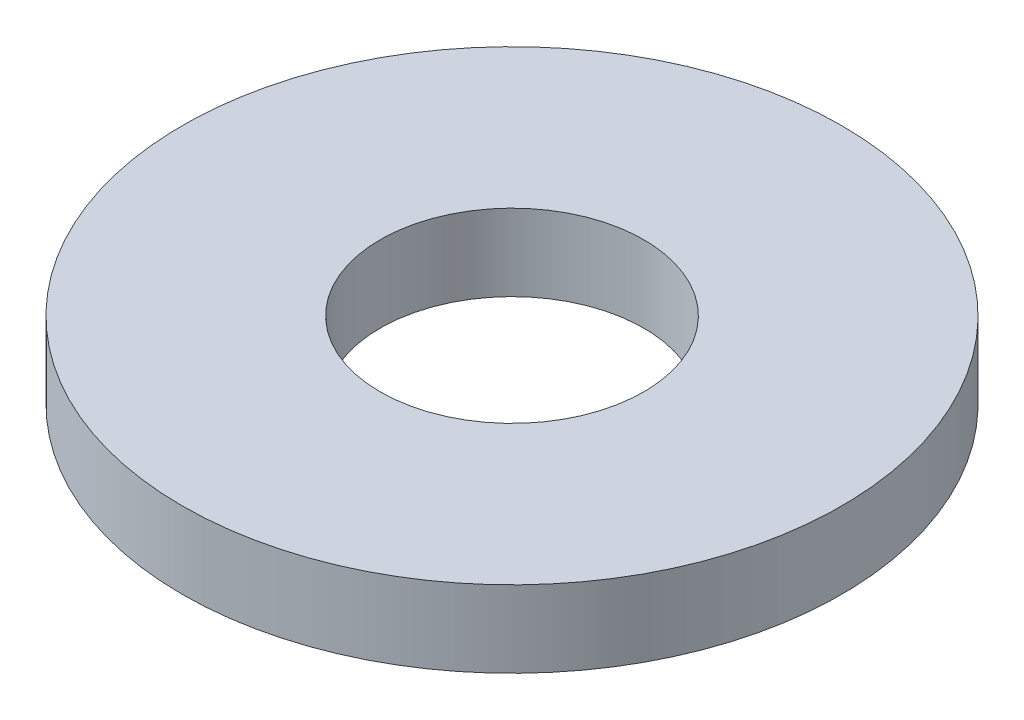
SolidWorks part; units mm, degrees
ref_plane "Front Plane" through (0, 0, 0) normal (0, 0, 1) x (1, 0, 0)
ref_plane "Top Plane" through (0, 0, 0) normal (0, 1, 0) x (1, 0, 0)
ref_plane "Right Plane" through (0, 0, 0) normal (1, 0, 0) x (0, 0, -1)
sketch "Sketch1" plane through (0, 0, 0) normal (0, 1, 0) x (1, 0, 0)
  circle A0 centre (0, 0) radius 1.6
  circle A1 centre (0, 0) radius 4
  dimension "D1" = 3.2
  dimension "D2" = 8
extrude "Boss-Extrude1" add sketch "Sketch1" along normal blind 0.93
